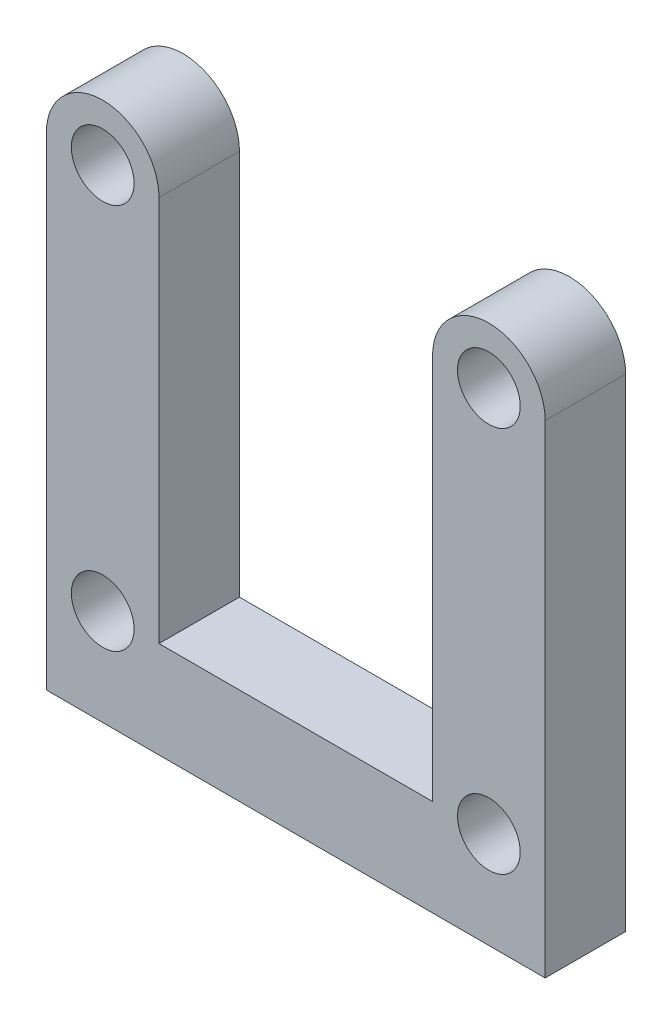
SolidWorks part; units mm, degrees
ref_plane "Ebene vorne" through (0, 0, 0) normal (0, 0, 1) x (1, 0, 0)
ref_plane "Ebene oben" through (0, 0, 0) normal (0, 1, 0) x (1, 0, 0)
ref_plane "Ebene rechts" through (0, 0, 0) normal (1, 0, 0) x (0, 0, -1)
sketch "Sketch1" plane through (0, 0, 0) normal (0, 0, 1) x (1, 0, 0)
  line L0 (-15.5, 12) -> (-15.5, -12.9711)
  line L2 (12, -12) -> (12, 12) construction
  line L3 (12, 12) -> (-12, 12) construction
  line L4 (-12, -12) -> (-12, 12) construction
  line L5 (12, -12) -> (-12, 12) construction
  line L6 (12, 12) -> (-12, -12) construction
  line L7 (15.5, 12) -> (15.5, -12)
  line L8 (8.5, 12) -> (8.5, -12)
  line L9 (-8.5, 12) -> (-8.5, -12)
  line L10 (0, 0) -> (0, -12) construction
  line L16 (8.5, -12) -> (-8.5, -12) construction
  line L17 (0, -18) -> (-15.5, -18)
  line L22 (0, -12) -> (-8.5, -12)
  line L23 (-15.5, -18) -> (-15.5, -12)
  line L24 (0, -12) -> (8.5, -12)
  line L26 (0, -18) -> (15.5, -18)
  line L27 (15.5, -12) -> (15.5, -18)
  circle A0 centre (-12, 12) radius 1.95
  circle A1 centre (12, 12) radius 1.95
  circle A2 centre (12, -12) radius 1.95
  arc A4 (-8.5, 12) -> (-15.5, 12) centre (-12, 12) ccw
  arc A5 (15.5, 12) -> (8.5, 12) centre (12, 12) ccw
  circle A8 centre (-12, -12) radius 1.95
  point P0 (0, 0)
  dimension "D3" = 3.9
  dimension "D4" = 7
  dimension "D1" = 24
  dimension "D2" = 24
  dimension "D5" = 18
extrude "Boss-Extrude1" add sketch "Sketch1" along normal blind 5
sketch "Sketch4" plane through (0, -18, 0) normal (0, -1, 0) x (1, 0, 0)
  line L0 (-15.5, 2.5) -> (15.5, 2.5) construction
  line L1 (-15.5, 5) -> (-15.5, 0) construction
  line L2 (15.5, 5) -> (15.5, 0) construction
  circle A0 centre (-8, 2.5) radius 1.25
  circle A1 centre (8, 2.5) radius 1.25
  dimension "D1" = 2.5
  dimension "D2" = 2.5
  dimension "D3" = 8
  dimension "D4" = 8
extrude "Cut-Extrude3" cut sketch "Sketch4" against normal blind 5.5
